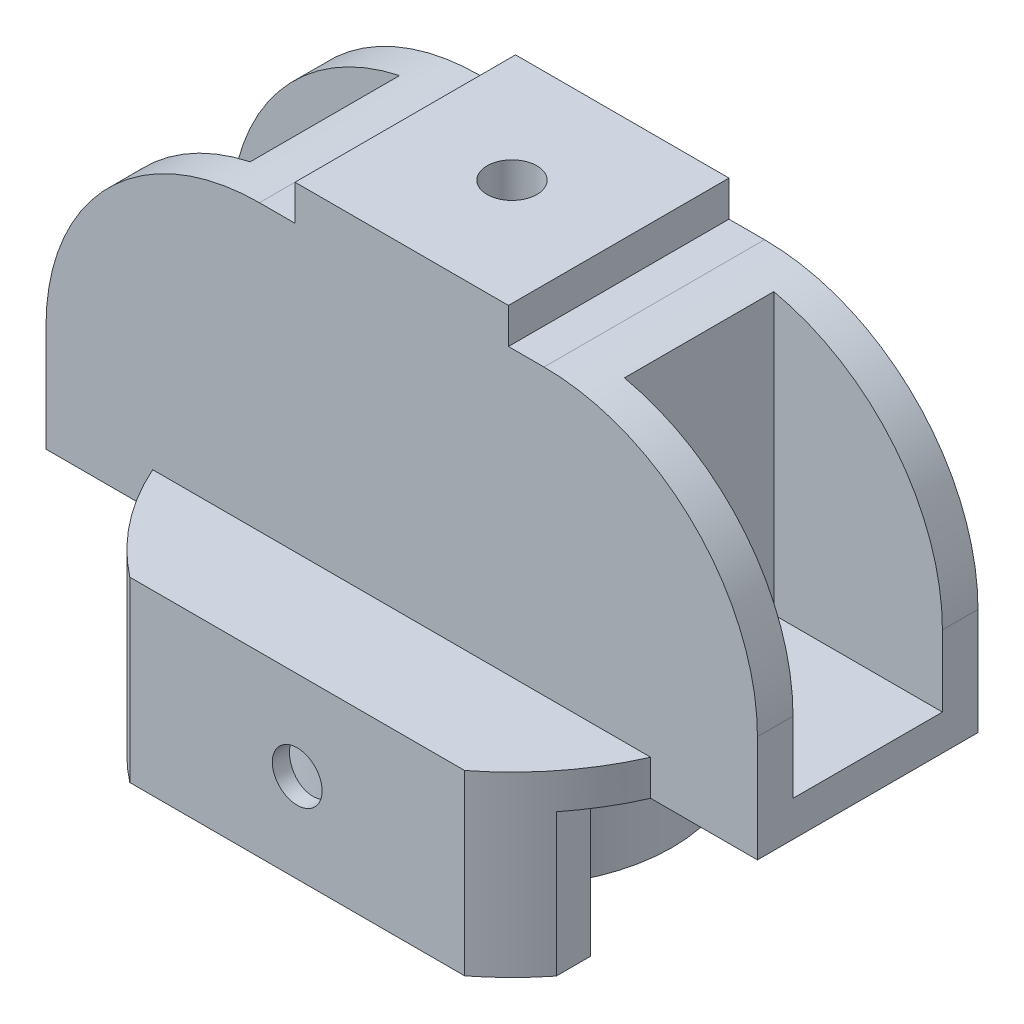
SolidWorks part; units mm, degrees
ref_plane "Front Plane" through (0, 0, 0) normal (0, 0, 1) x (1, 0, 0)
ref_plane "Top Plane" through (0, 0, 0) normal (0, 1, 0) x (1, 0, 0)
ref_plane "Right Plane" through (0, 0, 0) normal (1, 0, 0) x (0, 0, -1)
sketch "Sketch1" plane through (0, 0, 0) normal (0, 1, 0) x (1, 0, 0)
  circle A0 centre (0, 0) radius 22.5
  circle A1 centre (0, 0) radius 17.5
  dimension "D1" = 45
  dimension "D2" = 35
extrude "Boss-Extrude1" add sketch "Sketch1" along normal blind 20
sketch "Sketch2" plane through (0, 20, 0) normal (0, 1, 0) x (1, 0, 0)
  line L1 (-30, 19) -> (30, 19)
  line L2 (-30, 19) -> (-30, -19)
  line L3 (-30, -19) -> (30, -19)
  line L4 (30, 19) -> (30, -19)
  line L5 (-30, 19) -> (30, -19) construction
  line L6 (-30, -19) -> (30, 19) construction
  line L7 (-30, 30.189) -> (30, 30.189)
  line L8 (-30, 30.189) -> (-30, -30.189)
  line L9 (-30, -30.189) -> (30, -30.189)
  line L10 (30, 30.189) -> (30, -30.189)
  line L11 (-30, 30.189) -> (30, -30.189) construction
  line L12 (-30, -30.189) -> (30, 30.189) construction
  circle A0 centre (0, 0) radius 28
  point P0 (0, 0)
  dimension "D3" = 56
  dimension "D1" = 38
  dimension "D2" = 60
  dimension "D4" = 60
extrude "Boss-Extrude5" add sketch "Sketch2" against normal blind 20 separate body contours A0 L3 L8 L9 L10 | A0 L1 L10 L7 L8
sketch "Sketch5" plane through (0, 20, 0) normal (0, 1, 0) x (1, 0, 0)
  line L1 (-35, 30.189) -> (35, 30.189)
  line L2 (-35, 30.189) -> (-35, -30.189)
  line L3 (-35, -30.189) -> (35, -30.189)
  line L4 (35, 30.189) -> (35, -30.189)
  point P4 (0, -30.189)
  point P6 (0, 0)
  point P7 (0, 0)
  dimension "D1" = 70
extrude "Boss-Extrude7" add sketch "Sketch5" along normal blind 5
sketch "Sketch6" plane through (0, 25, 0) normal (0, 1, 0) x (1, 0, 0)
  line L1 (-50, 10.5) -> (50, 10.5)
  line L2 (-50, 10.5) -> (-50, -10.5)
  line L3 (-50, -10.5) -> (50, -10.5)
  line L4 (50, 10.5) -> (50, -10.5)
  line L5 (-50, 10.5) -> (50, -10.5) construction
  line L6 (-50, -10.5) -> (50, 10.5) construction
  line L7 (-26.3, 10.5) -> (26.3, 10.5)
  line L8 (-26.3, 10.5) -> (-26.3, -10.5)
  line L9 (-26.3, -10.5) -> (26.3, -10.5)
  line L10 (26.3, 10.5) -> (26.3, -10.5)
  line L11 (-26.3, 10.5) -> (26.3, -10.5) construction
  line L12 (-26.3, -10.5) -> (26.3, 10.5) construction
  line L13 (-50, 15.5) -> (50, 15.5)
  line L14 (-50, 15.5) -> (-50, -15.5)
  line L15 (-50, -15.5) -> (50, -15.5)
  line L16 (50, 15.5) -> (50, -15.5)
  line L17 (-50, 15.5) -> (50, -15.5) construction
  line L18 (-50, -15.5) -> (50, 15.5) construction
  point P0 (0, 0)
  point P6 (0, 0)
  point P11 (0, 0)
  line M5 (-35, 30.189) -> (-35, -30.189)
  line M7 (35, -30.189) -> (35, 30.189)
  dimension "D1" = 21
  dimension "D2" = 100
  dimension "D3" = 52.6
  dimension "D4" = 31
  dimension "D5" = 100
extrude "Boss-Extrude8" add sketch "Sketch6" along normal blind 40 contours L15 L3 M5 M7 | L16 L3 L15 M7 | L14 L15 L3 M5 | L13 L14 L1 M5 | L13 L1 M5 M7 | L16 L13 L1 M7 | L10 L1 L8 L3
sketch "Sketch7" plane through (0, 25, 0) normal (0, -1, 0) x (1, 0, 0)
  line L1 (-50, 15.5) -> (50, 15.5)
  line L2 (-50, 15.5) -> (-50, -15.5)
  line L3 (-50, -15.5) -> (50, -15.5)
  line L4 (50, 15.5) -> (50, -15.5)
extrude "Boss-Extrude9" add sketch "Sketch7" along normal blind 5
sketch "Sketch8" plane through (0, 0, 0) normal (0, -1, 0) x (1, 0, 0)
  line L0 (35, -15.5) -> (50, -15.5) construction
  line L1 (-57.7537, 15.5) -> (57.7537, 15.5)
  line L2 (-57.7537, 15.5) -> (-57.7537, -15.5)
  line L3 (-57.7537, -15.5) -> (57.7537, -15.5)
  line L4 (57.7537, 15.5) -> (57.7537, -15.5)
  line L5 (-57.7537, 15.5) -> (57.7537, -15.5) construction
  line L6 (-57.7537, -15.5) -> (57.7537, 15.5) construction
  circle A0 centre (0, 0) radius 38.2786
  circle A1 centre (0, 0) radius 50.7446
extrude "Cut-Extrude1" cut sketch "Sketch8" against normal through all both and the other way through all contours L1 A1 A0 | L3 A1 A0
fillet "Fillet1" radius 30 2 edges at (-50, 65, -13) (50, 65, 13)
sketch "Sketch9" plane through (0, 65, 0) normal (0, 1, 0) x (1, 0, 0)
  line L0 (-20, -15.5) -> (20, -15.5) construction
  line L1 (-15, 15.5) -> (15, 15.5)
  line L2 (-15, 15.5) -> (-15, -15.5)
  line L3 (-15, -15.5) -> (15, -15.5)
  line L4 (15, 15.5) -> (15, -15.5)
  line L5 (-15, 15.5) -> (15, -15.5) construction
  line L6 (-15, -15.5) -> (15, 15.5) construction
  point P0 (0, 0)
  dimension "D1" = 30
extrude "Boss-Extrude10" add sketch "Sketch9" along normal blind 5
sketch "Sketch10" plane through (0, 70, 0) normal (0, 1, 0) x (1, 0, 0)
  circle A0 centre (0, 0) radius 3.5
  dimension "D1" = 7
extrude "Cut-Extrude2" cut sketch "Sketch10" against normal through all
sketch "Sketch11" plane through (0, 20, 0) normal (0, -1, 0) x (1, 0, 0)
  circle A0 centre (0, 0) radius 12.5
  dimension "D1" = 25
extrude "Cut-Extrude3" cut sketch "Sketch11" against normal blind 45
sketch "Sketch12" plane through (0, 0, 30.189) normal (0, 0, 1) x (1, 0, 0)
  line L2 (23.5345, 25) -> (23.5345, 0) construction
  circle A0 centre (0, 12.5) radius 3.5
  point P5 (23.5345, 12.5)
  point P7 (0, 0)
  dimension "D1" = 7
extrude "Cut-Extrude4" cut sketch "Sketch12" against normal through all
